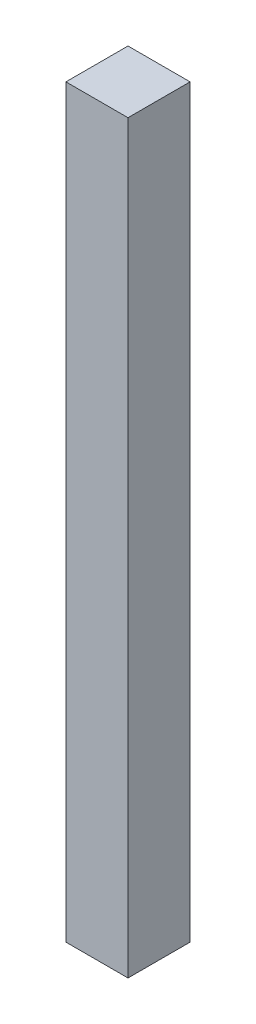
SolidWorks part; units mm, degrees
ref_plane "Front Plane" through (0, 0, 0) normal (0, 0, 1) x (1, 0, 0)
ref_plane "Top Plane" through (0, 0, 0) normal (0, 1, 0) x (1, 0, 0)
ref_plane "Right Plane" through (0, 0, 0) normal (1, 0, 0) x (0, 0, -1)
sketch "Sketch1" plane through (0, 0, 0) normal (0, 1, 0) x (1, 0, 0)
  line L1 (-6.6679, 5.36) -> (18.7321, 5.36)
  line L2 (-6.6679, 5.36) -> (-6.6679, -20.04)
  line L3 (-6.6679, -20.04) -> (18.7321, -20.04)
  line L4 (18.7321, 5.36) -> (18.7321, -20.04)
  dimension "D1" = 25.4
  dimension "D2" = 25.4
extrude "Boss-Extrude1" add sketch "Sketch1" along normal blind 304.8
